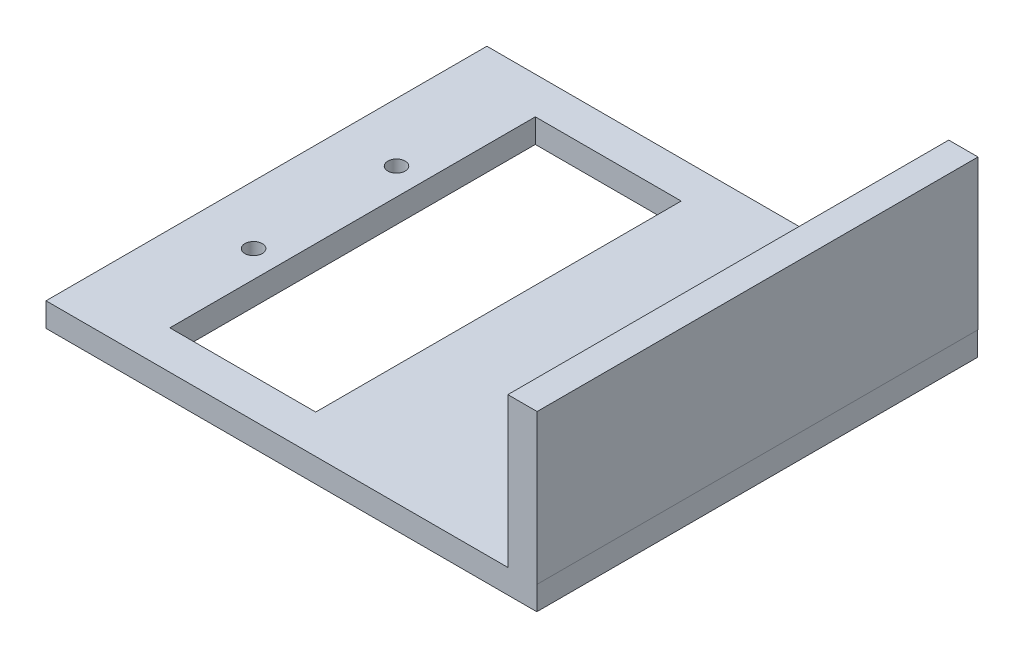
SolidWorks part; units mm, degrees
ref_plane "Front Plane" through (0, 0, 0) normal (0, 0, 1) x (1, 0, 0)
ref_plane "Top Plane" through (0, 0, 0) normal (0, 1, 0) x (1, 0, 0)
ref_plane "Right Plane" through (0, 0, 0) normal (1, 0, 0) x (0, 0, -1)
sketch "Sketch1" plane through (0, 0, 0) normal (0, 1, 0) x (1, 0, 0)
  line L1 (-40.3324, 34.6721) -> (41.6676, 34.6721)
  line L2 (-40.3324, 34.6721) -> (-40.3324, -38.9879)
  line L3 (-40.3324, -38.9879) -> (41.6676, -38.9879)
  line L4 (41.6676, 34.6721) -> (41.6676, -38.9879)
extrude "Boss-Extrude1" add sketch "Sketch1" along normal blind 4
sketch "Sketch2" plane through (0, 4, 0) normal (0, 1, 0) x (1, 0, 0)
  line L1 (36.8283, 34.6721) -> (41.7155, 34.6721)
  line L2 (36.8283, 34.6721) -> (36.8283, -38.9879)
  line L3 (36.8283, -38.9879) -> (41.7155, -38.9879)
  line L4 (41.7155, 34.6721) -> (41.7155, -38.9879)
  line L5 (41.6676, 34.6721) -> (-40.3324, 34.6721) construction
  point P5 (35.3935, 34.6721)
  point P7 (41.6676, 34.6721)
extrude "Boss-Extrude2" add sketch "Sketch2" along normal blind 25
sketch "Sketch3" plane through (0, 4, 0) normal (0, 1, 0) x (1, 0, 0)
  line L0 (-30.5441, -2.1579) -> (-30.5441, -14.0979) construction
  line L1 (-40.2041, 34.6721) -> (-40.2041, -38.9879) construction
  line L2 (36.8283, 34.6721) -> (-40.3324, 34.6721) construction
  line L3 (-40.3324, -38.9879) -> (36.8283, -38.9879) construction
  line L4 (-40.2041, -2.1579) -> (-30.5441, -2.1579) construction
  line L5 (-30.5441, -2.1579) -> (-30.5441, 9.7821) construction
  circle A0 centre (-30.5441, 9.7821) radius 1.45
  circle A1 centre (-30.5441, -14.0979) radius 1.45
extrude "Cut-Extrude1" cut sketch "Sketch3" against normal blind 10
sketch "Sketch4" plane through (0, 4, 0) normal (0, 1, 0) x (1, 0, 0)
  line L1 (-1.7001, 28.5027) -> (-26.0701, 28.5027)
  line L2 (-1.7001, 28.5027) -> (-1.7001, -32.56)
  line L3 (-1.7001, -32.56) -> (-26.0701, -32.56)
  line L4 (-26.0701, 28.5027) -> (-26.0701, -32.56)
extrude "Cut-Extrude2" cut sketch "Sketch4" against normal blind 10
